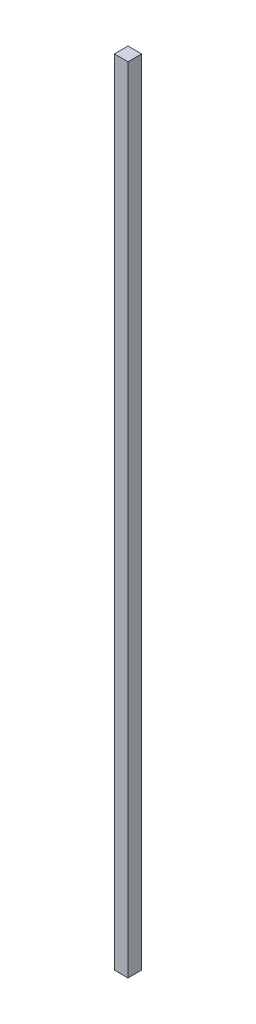
SolidWorks part; units mm, degrees
ref_plane "Plano frontal" through (0, 0, 0) normal (0, 0, 1) x (1, 0, 0)
ref_plane "Plano superior" through (0, 0, 0) normal (0, 1, 0) x (1, 0, 0)
ref_plane "Plano direito" through (0, 0, 0) normal (1, 0, 0) x (0, 0, -1)
sketch "Esboço2" plane through (0, 0, 0) normal (0, 1, 0) x (1, 0, 0)
  line L1 (-50, 29.0761) -> (0, 29.0761)
  line L2 (-50, 29.0761) -> (-50, -20.9239)
  line L3 (-50, -20.9239) -> (0, -20.9239)
  line L4 (0, 29.0761) -> (0, -20.9239)
  dimension "D1" = 50
  dimension "D2" = 50
extrude "Ressalto-extrusão1" add sketch "Esboço2" along normal blind 2900 contours L1 L4 L3 L2
